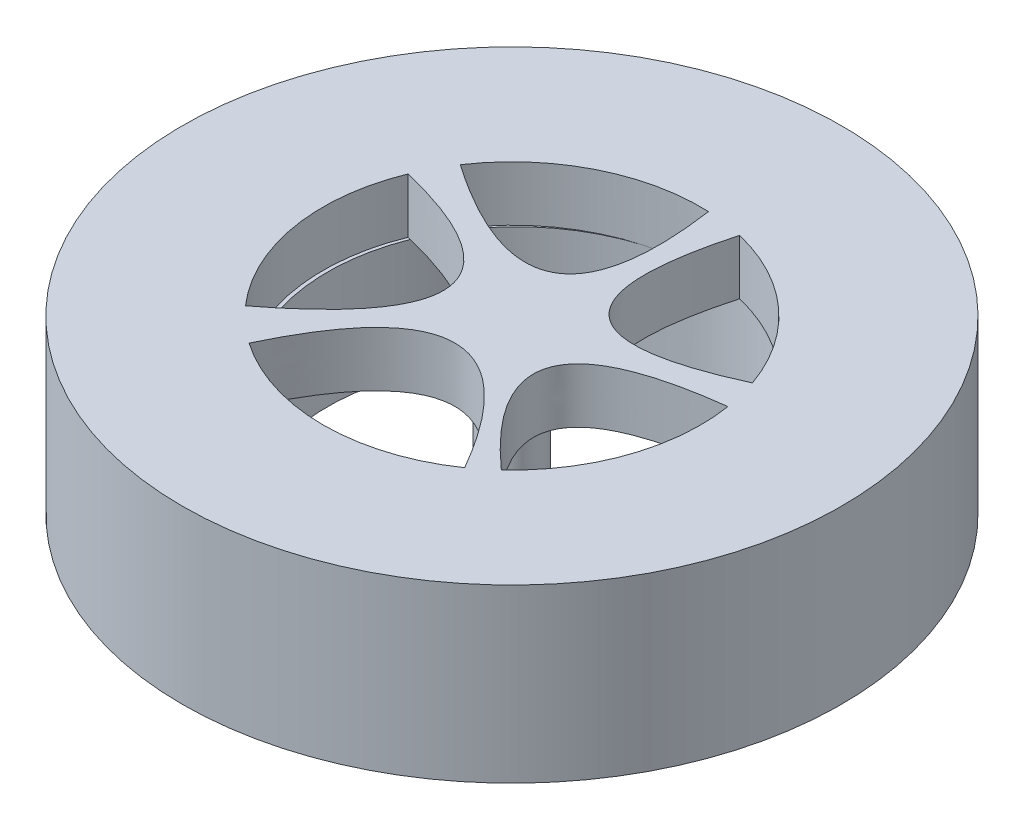
SolidWorks part; units mm, degrees
ref_plane "Front Plane" through (0, 0, 0) normal (0, 0, 1) x (1, 0, 0)
ref_plane "Top Plane" through (0, 0, 0) normal (0, 1, 0) x (1, 0, 0)
ref_plane "Right Plane" through (0, 0, 0) normal (1, 0, 0) x (0, 0, -1)
sketch "Sketch2" plane through (0, 0, 0) normal (0, 1, 0) x (1, 0, 0)
  circle A0 centre (-41.8687, 18.125) radius 40
  dimension "D1" = 80
extrude "Boss-Extrude1" add sketch "Sketch2" along normal blind 25
sketch "Sketch3" plane through (0, 0, 0) normal (0, -1, 0) x (1, 0, 0)
  circle A0 centre (-41.3458, -18.2744) radius 27.5
  dimension "D1" = 55
extrude "Cut-Extrude1" cut sketch "Sketch3" against normal blind 17 contours A0
sketch "Sketch4" plane through (0, 17, 0) normal (0, -1, 0) x (1, 0, 0)
  arc A0 (-14.7064, -22.4211) -> (-23.2105, 2.0771) centre (-41.8687, -18.125) ccw
  arc A1 (-35.4539, -44.8664) -> (-15.9046, -27.1868) centre (-41.8687, -18.125) ccw
  arc A2 (-64.7074, -33.4431) -> (-40.7179, -45.6009) centre (-41.8687, -18.125) ccw
  arc A3 (-62.5505, 0) -> (-67.3465, -28.4754) centre (-41.8687, -18.125) ccw
  arc A4 (-26.1745, 4.4569) -> (-57.5826, 4.4432) centre (-41.8687, -18.125) ccw
  spline S0 degree 2 poles (-40.7179, -45.6009) (-36.1565, -13.6021) (-64.7074, -33.4431) knots 0 0 0 1 1 1
  spline S1 degree 2 poles (-67.3465, -28.4754) (-35.3604, -20.7101) (-62.5505, 0) knots 0 0 0 1 1 1
  spline S2 degree 2 poles (-57.5826, 4.4432) (-43.3824, -25.5706) (-26.1745, 4.4569) knots 0 0 0 1 1 1
  spline S3 degree 2 poles (-23.2105, 2.0771) (-46.3557, -18.5465) (-14.7064, -22.4211) knots 0 0 0 1 1 1
  spline S4 degree 2 poles (-15.9046, -27.1868) (-43.8764, -14.3289) (-35.4539, -44.8664) knots 0 0 0 1 1 1
  point P7 (-43.4565, -27.1868)
  point P19 (-50.2969, -18.125)
  point P20 (-43.4565, -10.5189)
  point P21 (-32.7855, -13.9391)
  point P22 (-34.4272, -24.8837)
  dimension "D1" = 55
extrude "Cut-Extrude3" cut sketch "Sketch4" against normal through all
sketch "Sketch5" plane through (0, 17, 0) normal (0, -1, 0) x (1, 0, 0)
  circle A0 centre (-41.8687, -18.125) radius 4
  dimension "D1" = 8
extrude "Boss-Extrude3" add sketch "Sketch5" along normal blind 25
sketch "Sketch6" plane through (0, -8, 0) normal (0, -1, 0) x (1, 0, 0)
  circle A0 centre (-41.8687, -18.125) radius 2.5
  dimension "D1" = 5
extrude "Cut-Extrude4" cut sketch "Sketch6" against normal blind 10
sketch "Sketch9" plane through (0, 0, 0) normal (1, 0, 0) x (0, 0, -1)
sketch "Sketch18" plane through (0, 0, 0) normal (0, 1, 0) x (1, 0, 0)
  circle A0 centre (-41.8687, 18.125) radius 48
  circle A1 centre (-41.8687, 18.125) radius 40
  dimension "D1" = 96
extrude "Boss-Extrude5" add sketch "Sketch18" along normal blind 25
